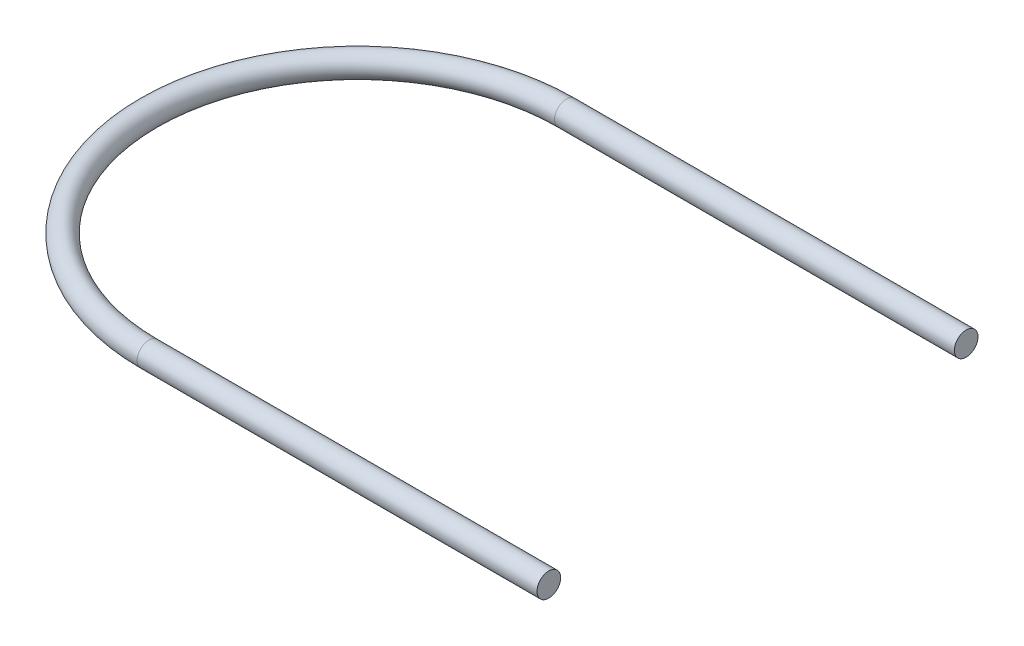
SolidWorks part; units mm, degrees
ref_plane "Front Plane" through (0, 0, 0) normal (0, 0, 1) x (1, 0, 0)
ref_plane "Top Plane" through (0, 0, 0) normal (0, 1, 0) x (1, 0, 0)
ref_plane "Right Plane" through (0, 0, 0) normal (1, 0, 0) x (0, 0, -1)
sketch "Sketch1" plane through (0, 0, 0) normal (0, 1, 0) x (1, 0, 0)
  line L0 (0, -7.85) -> (15.0409, -7.85)
  line L2 (7.1028, 11.8653) -> (7.1731, 11.9024)
  line L3 (0, 7.85) -> (15.0409, 7.85)
  arc A0 (0, 7.85) -> (0, -7.85) centre (0, 0) ccw
  dimension "D1" = 15.7
ref_plane "Plane1" through (15.0409, 0, 0) normal (1, 0, 0) x (0, 0, -1)
sketch "Sketch2" plane through (15.0409, 0, 0) normal (1, 0, 0) x (0, 0, -1)
  circle A0 centre (-7.85, 0) radius 0.4445
  dimension "D1" = 0.889
sweep "Sweep1" add profiles "Sketch2" path "Sketch1"
